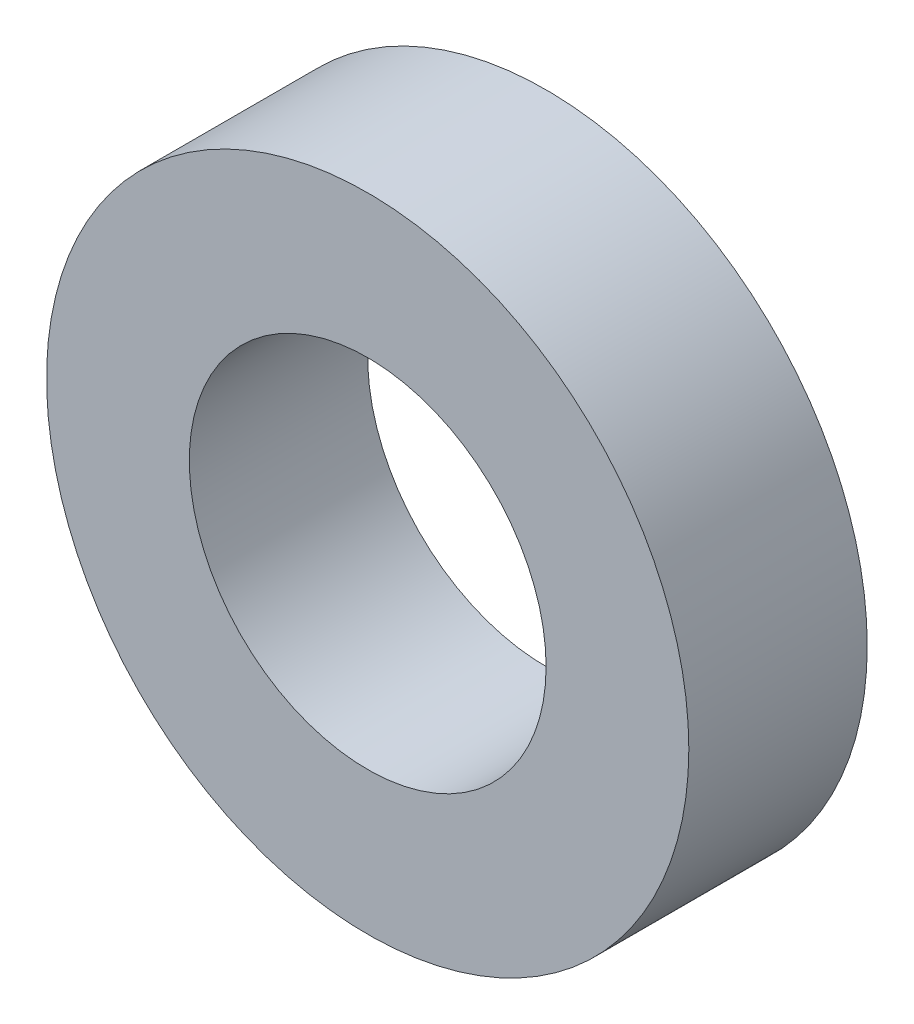
SolidWorks part; units mm, degrees
ref_plane "Ebene vorne" through (0, 0, 0) normal (0, 0, 1) x (1, 0, 0)
ref_plane "Ebene oben" through (0, 0, 0) normal (0, 1, 0) x (1, 0, 0)
ref_plane "Ebene rechts" through (0, 0, 0) normal (1, 0, 0) x (0, 0, -1)
sketch "Skizze1" plane through (0, 0, 0) normal (0, 0, 1) x (1, 0, 0)
  circle A0 centre (0, 0) radius 15
  circle A1 centre (0, 0) radius 27
  dimension "D1" = 30
  dimension "D2" = 54
extrude "Aufsatz-Linear austragen1" add sketch "Skizze1" along normal blind 15
